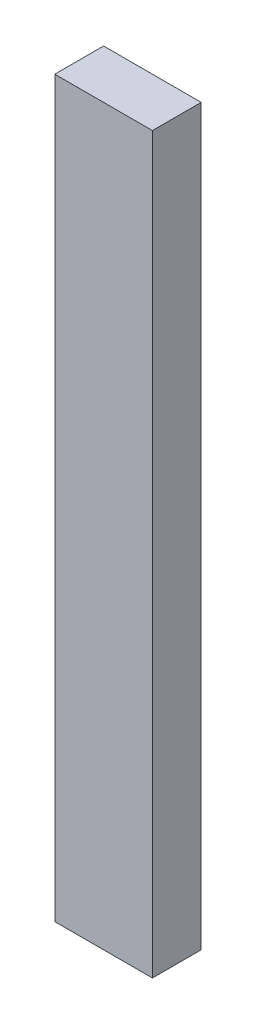
SolidWorks part; units mm, degrees
ref_plane "Front Plane" through (0, 0, 0) normal (0, 0, 1) x (1, 0, 0)
ref_plane "Top Plane" through (0, 0, 0) normal (0, 1, 0) x (1, 0, 0)
ref_plane "Right Plane" through (0, 0, 0) normal (1, 0, 0) x (0, 0, -1)
sketch "Sketch1" plane through (0, 0, 0) normal (0, 0, 1) x (1, 0, 0)
  line L1 (0, 0) -> (101.6, 0)
  line L2 (0, 0) -> (0, 763.794)
  line L3 (0, 763.794) -> (101.6, 763.794)
  line L4 (101.6, 0) -> (101.6, 763.794)
  dimension "D1" = 763.794
  dimension "D2" = 101.6
extrude "Boss-Extrude1" add sketch "Sketch1" along normal mid plane 50.8
